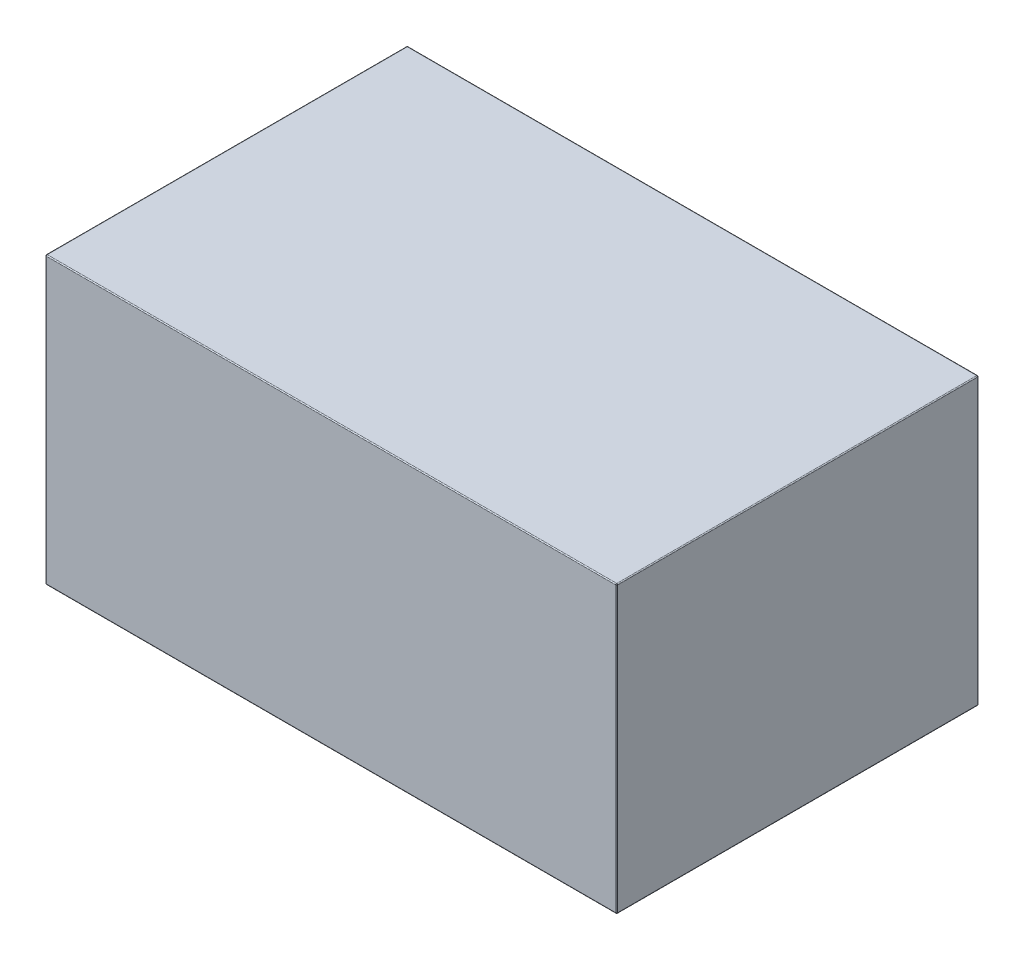
SolidWorks part; units mm, degrees
ref_plane "Front Plane" through (0, 0, 0) normal (0, 0, 1) x (1, 0, 0)
ref_plane "Top Plane" through (0, 0, 0) normal (0, 1, 0) x (1, 0, 0)
ref_plane "Right Plane" through (0, 0, 0) normal (1, 0, 0) x (0, 0, -1)
sketch "Sketch1" plane through (0, 0, 0) normal (0, 1, 0) x (1, 0, 0)
  line L1 (-76.2, 48.26) -> (76.2, 48.26)
  line L2 (-76.2, 48.26) -> (-76.2, -48.26)
  line L3 (-76.2, -48.26) -> (76.2, -48.26)
  line L4 (76.2, 48.26) -> (76.2, -48.26)
  line L5 (-76.2, 48.26) -> (76.2, -48.26) construction
  line L6 (-76.2, -48.26) -> (76.2, 48.26) construction
  point P0 (0, 0)
  dimension "D1" = 96.52
  dimension "D2" = 152.4
extrude "Boss-Extrude1" add sketch "Sketch1" along normal mid plane 76.2
fillet "Fillet1" radius 0.254 12 edges at (-76.2, -38.1, 0) (-76.2, 0, -48.26) (0, -38.1, -48.26) (76.2, 0, -48.26) (76.2, -38.1, 0) (-76.2, 0, 48.26) (76.2, 0, 48.26) (0, -38.1, 48.26) (0, 38.1, 48.26) (-76.2, 38.1, 0) (0, 38.1, -48.26) (76.2, 38.1, 0)
